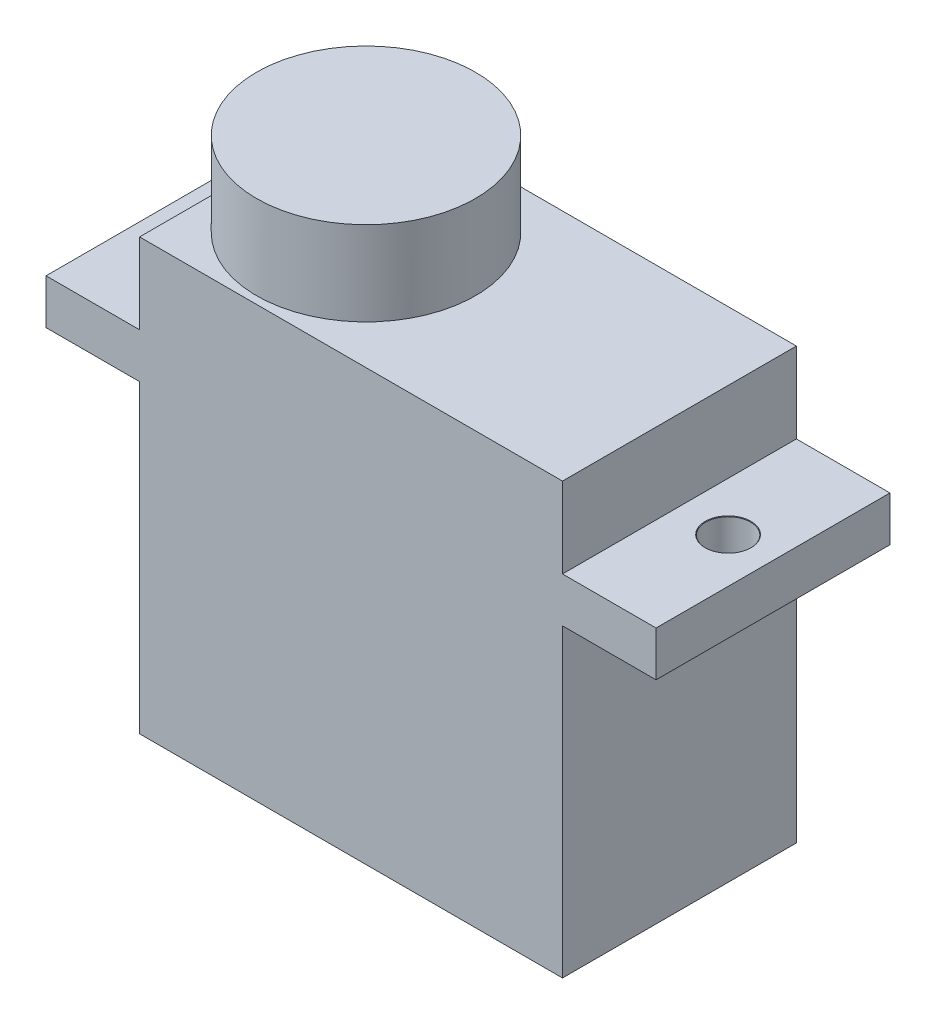
SolidWorks part; units mm, degrees
ref_plane "Front Plane" through (0, 0, 0) normal (0, 0, 1) x (1, 0, 0)
ref_plane "Top Plane" through (0, 0, 0) normal (0, 1, 0) x (1, 0, 0)
ref_plane "Right Plane" through (0, 0, 0) normal (1, 0, 0) x (0, 0, -1)
sketch "Sketch1" plane through (0, 0, 0) normal (0, 1, 0) x (1, 0, 0)
  line L1 (11.3, 6.25) -> (-11.3, 6.25)
  line L2 (11.3, 6.25) -> (11.3, -6.25)
  line L3 (11.3, -6.25) -> (-11.3, -6.25)
  line L4 (-11.3, 6.25) -> (-11.3, -6.25)
  line L5 (11.3, 6.25) -> (-11.3, -6.25) construction
  line L6 (11.3, -6.25) -> (-11.3, 6.25) construction
  point P0 (0, 0)
  dimension "D1" = 22.6
  dimension "D2" = 12.5
extrude "Boss-Extrude1" add sketch "Sketch1" along normal blind 23
ref_plane "Plane1" through (0, 18.7, 0) normal (0, 1, 0) x (1, 0, 0)
sketch "Sketch2" plane through (0, 18.7, 0) normal (0, 1, 0) x (1, 0, 0)
  line L0 (11.3, -6.25) -> (11.3, 6.25) construction
  line L1 (-11.3, 6.25) -> (-11.3, -6.25) construction
  line L2 (11.3, -6.25) -> (11.3, 6.25)
  line L3 (-11.3, 6.25) -> (-11.3, -6.25)
  line L4 (-11.3, 6.25) -> (-16.3, 6.25)
  line L5 (-16.3, 6.25) -> (-16.3, -6.25)
  line L6 (-16.3, -6.25) -> (-11.3, -6.25)
  line L7 (11.3, 6.25) -> (16.3, 6.25)
  line L8 (16.3, 6.25) -> (16.3, -6.25)
  line L9 (16.3, -6.25) -> (11.3, -6.25)
  dimension "D1" = 5
extrude "Boss-Extrude2" add sketch "Sketch2" against normal blind 2.4
hole_wizard "M2 Clearance Hole1" positions "Sketch3" profile "Sketch4" hole size "M2" standard "ANSI Metric"
sketch "Sketch3" plane through (0, 18.7, 0) normal (0, 1, 0) x (1, 0, 0)
  line L0 (-13.9, 0) -> (13.9, 0) construction
  point P0 (-13.9, 0)
  point P2 (13.9, 0)
  point P12 (0, 0)
  point P13 (-14.5025, 0)
  point P14 (0, 0)
  dimension "D1" = 27.8
sketch "Sketch4" plane through (-13.9, 18.7, 0) normal (1, 0, 0) x (0, 0, 1)
  line L0 (0, 0) -> (0, 22.231)
  line L1 (0, 22.231) -> (1.2, 21.51)
  line L2 (1.2, 21.51) -> (1.2, 0.025)
  line L3 (1.2, 0.025) -> (1.225, 0)
  line L5 (1.225, 0) -> (0, 0)
  line L6 (-1.2, 0.025) -> (-1.225, 0) construction
  line L10 (0, 22.231) -> (-1.2, 21.51) construction
  line L11 (0, -6.35) -> (0, 107.95) construction
  dimension "Hole Dia." = 2.4
  dimension "Hole Depth" = 21.51
  dimension "Near C'Sink Dia." = 2.45
  dimension "Near C'Sink Angle" = 90
  dimension "Drill Angle" = 118
sketch "Sketch5" plane through (0, 23, 0) normal (0, 1, 0) x (1, 0, 0)
  line L0 (-11.3, -6.25) -> (-11.3, 6.25) construction
  circle A0 centre (-5.45, 0) radius 5.85
  dimension "D1" = 11.7
extrude "Boss-Extrude3" add sketch "Sketch5" along normal blind 4.5
